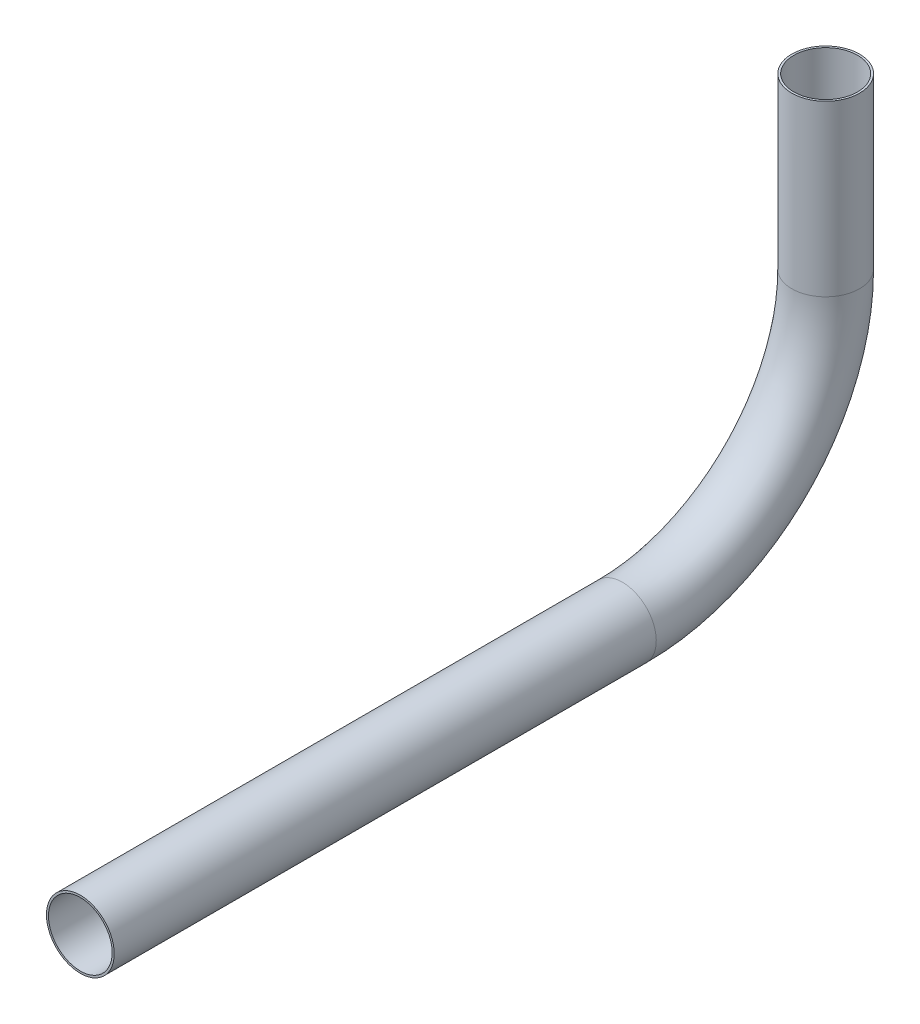
SolidWorks part; units mm, degrees
ref_plane "Front Plane" through (0, 0, 0) normal (0, 0, 1) x (1, 0, 0)
ref_plane "Top Plane" through (0, 0, 0) normal (0, 1, 0) x (1, 0, 0)
ref_plane "Right Plane" through (0, 0, 0) normal (1, 0, 0) x (0, 0, -1)
sketch "Sketch1" plane through (0, 0, 0) normal (0, 1, 0) x (1, 0, 0)
  circle A0 centre (0, 0) radius 6.35
  circle A1 centre (0, 0) radius 5.969
  dimension "D1" = 12.7
  dimension "D2" = 11.938
sketch "Sketch2" plane through (0, 0, 0) normal (1, 0, 0) x (0, 0, -1)
  line L0 (0, 0) -> (0, -31.75)
  line L1 (-38.1, -69.85) -> (-139.7, -69.85)
  arc A0 (0, -31.75) -> (-38.1, -69.85) centre (-38.1, -31.75) cw
  dimension "D3" = 38.1
  dimension "D1" = 31.75
  dimension "D2" = 101.6
sweep "Sweep1" add profiles "Sketch1" path "Sketch2"
